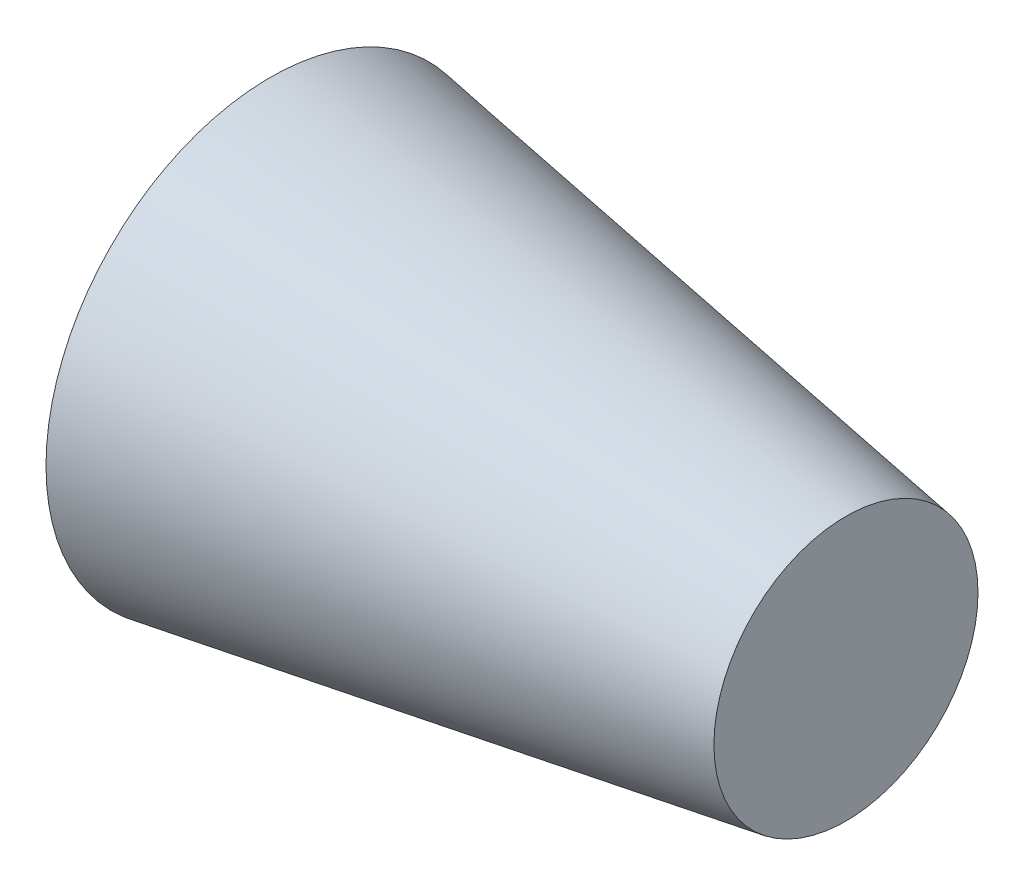
SolidWorks part; units mm, degrees
ref_plane "Plano frontal" through (0, 0, 0) normal (0, 0, 1) x (1, 0, 0)
ref_plane "Plano superior" through (0, 0, 0) normal (0, 1, 0) x (1, 0, 0)
ref_plane "Plano direito" through (0, 0, 0) normal (1, 0, 0) x (0, 0, -1)
other "Center of Mass"
sketch "Sketch1" plane through (0, 0, 0) normal (0, 0, 1) x (1, 0, 0)
  line L0 (380.587, 265.4331) -> (1380.587, 265.4331) construction
  line L1 (85.3379, 164.3007) -> (23275.3379, 164.3007) construction
  line L2 (222.9986, 147.9748) -> (23412.9986, 147.9748) construction
  line L3 (17192.2399, 1293.6021) -> (17192.2399, -967.3859)
  line L4 (17192.2399, 163.1081) -> (20094.5355, 163.1081) construction
  line L5 (20094.5355, -502.5486) -> (20094.5355, 828.7648)
  line L6 (17192.2399, -967.3859) -> (20094.5355, -502.5486)
  line L7 (20094.5355, 828.7648) -> (17192.2399, 1293.6021)
  line L8 (17192.2399, 163.1081) -> (20094.5355, 163.1081)
  point P13 (20094.5355, 163.1081)
  dimension "D1" = 1000
  dimension "D2" = 23190
  dimension "D3" = 23190
  dimension "D4" = 2260.988
  dimension "D5" = 1331.3133
  dimension "D6" = 2902.2956
revolve "Revolve1" add sketch "Sketch1" angle 360 about L4
sketch "Sketch2" plane through (0, 0, 0) normal (0, 0, 1) x (1, 0, 0)
  line L1 (17192.2399, 163.1081) -> (20094.5355, 163.1081) construction
  point P0 (232.9164, 134.5558)
  point P1 (18400, 163.1081)
  point P2 (0, 0)
  dimension "D1" = 18400
  dimension "D2" = 18167.0836
